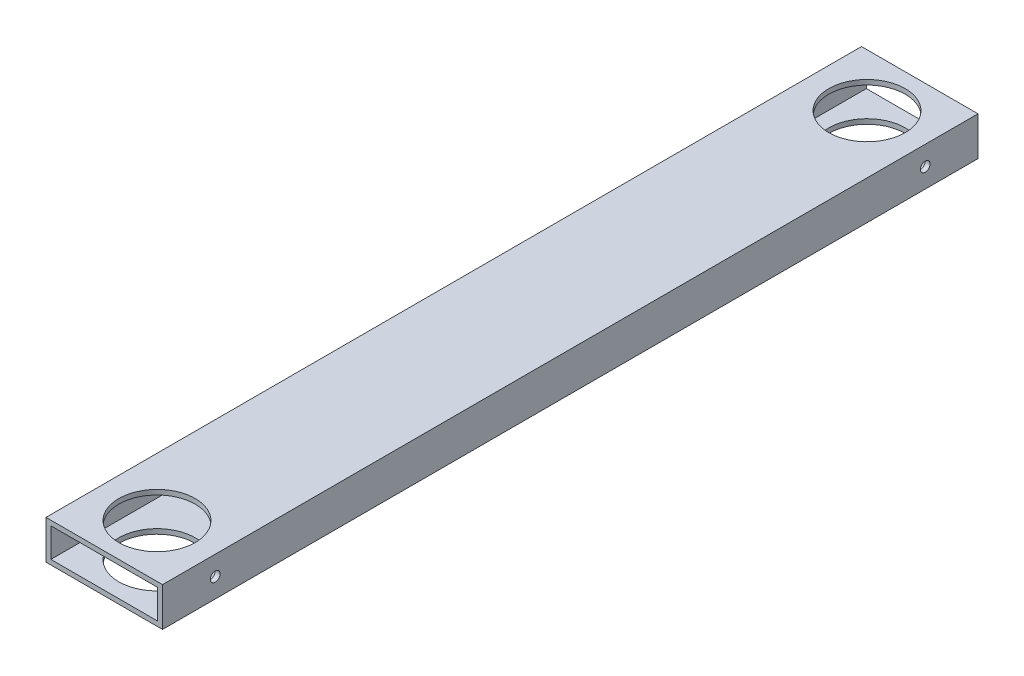
SolidWorks part; units mm, degrees
ref_plane "Front" through (0, 0, 0) normal (0, 0, 1) x (1, 0, 0)
ref_plane "Top" through (0, 0, 0) normal (0, 1, 0) x (1, 0, 0)
ref_plane "Right" through (0, 0, 0) normal (1, 0, 0) x (0, 0, -1)
sketch "Sketch1" plane through (0, 0, 0) normal (0, 0, 1) x (1, 0, 0)
  line L1 (-38.1, -12.7) -> (38.1, -12.7)
  line L2 (-38.1, -12.7) -> (-38.1, 12.7)
  line L3 (-38.1, 12.7) -> (38.1, 12.7)
  line L4 (38.1, -12.7) -> (38.1, 12.7)
  line L5 (-38.1, -12.7) -> (38.1, 12.7) construction
  line L6 (-38.1, 12.7) -> (38.1, -12.7) construction
  point P0 (0, 0)
  dimension "D1" = 25.4
  dimension "D2" = 76.2
extrude "Extrude-Thin1" add sketch "Sketch1" along normal blind 533.4 thin thin type one direction reverse wall 3.175
sketch "Sketch3" plane through (0, 12.7, 0) normal (0, 1, 0) x (1, 0, 0)
  line L0 (0, -498.903) -> (0, 0) construction
  line L2 (38.1, 0) -> (-38.1, 0) construction
  line L3 (24.972, -34.497) -> (24.972, 0) construction
  line L4 (-34.925, 0) -> (-34.925, -74.0391) construction
  line L5 (-38.1, -533.4) -> (-38.1, 0) construction
  line L6 (38.1, -533.4) -> (-38.1, -533.4) construction
  line L7 (-12.9866, -7.9375) -> (-34.925, -7.9375)
  line L8 (0, -34.497) -> (0, 0) construction
  line L9 (0, -498.903) -> (0, -533.4) construction
  line L11 (-12.9866, -61.0565) -> (-34.925, -61.0565)
  line L12 (-34.925, -61.0565) -> (-34.925, -7.9375)
  line L14 (-38.1, -12.7) -> (38.1, -12.7) construction
  line L15 (38.1, -533.4) -> (38.1, 0) construction
  circle A0 centre (0, -498.903) radius 24.972
  circle A1 centre (0, -34.497) radius 24.972
  arc A2 (-12.2542, -10.9334) -> (-12.2542, -58.0606) centre (0, -34.497) ccw
  arc A3 (-12.9866, -7.9375) -> (-12.2542, -10.9334) centre (-12.9866, -9.525) cw
  arc A4 (-12.2542, -58.0606) -> (-12.9866, -61.0565) centre (-12.9866, -59.469) cw
  point P0 (0, -9.525)
  point P14 (0, -523.875)
  point P22 (-26.5595, -34.497)
  point P27 (0, -7.9375)
  point P30 (0, -61.0565)
  dimension "D1" = 9.525
  dimension "D2" = 49.944
  dimension "D5" = 1.5875
  dimension "D6" = 1.5875
  dimension "D4" = 3.175
extrude "Cut-Extrude2" cut sketch "Sketch3" against normal through all contours A1 | A0
sketch "Sketch4" plane through (38.1, 0, 0) normal (1, 0, 0) x (0, 0, -1)
  line L0 (0, 0) -> (-34.497, 0) construction
  line L1 (0, -12.7) -> (0, 12.7) construction
  line L2 (-266.7, 12.7) -> (-266.7, -12.7) construction
  line L3 (-533.4, 12.7) -> (0, 12.7) construction
  line L4 (-533.4, -12.7) -> (0, -12.7) construction
  line L5 (-9.525, 12.7) -> (-59.469, 12.7) construction
  line L6 (-9.525, 12.7) -> (-59.469, 12.7) construction
  line L7 (-34.497, 12.7) -> (-34.497, 0) construction
  circle A0 centre (-34.497, 0) radius 3.175
  circle A1 centre (-498.903, 0) radius 3.175
  dimension "D2" = 6.35
extrude "Cut-Extrude3" cut sketch "Sketch4" against normal through all
